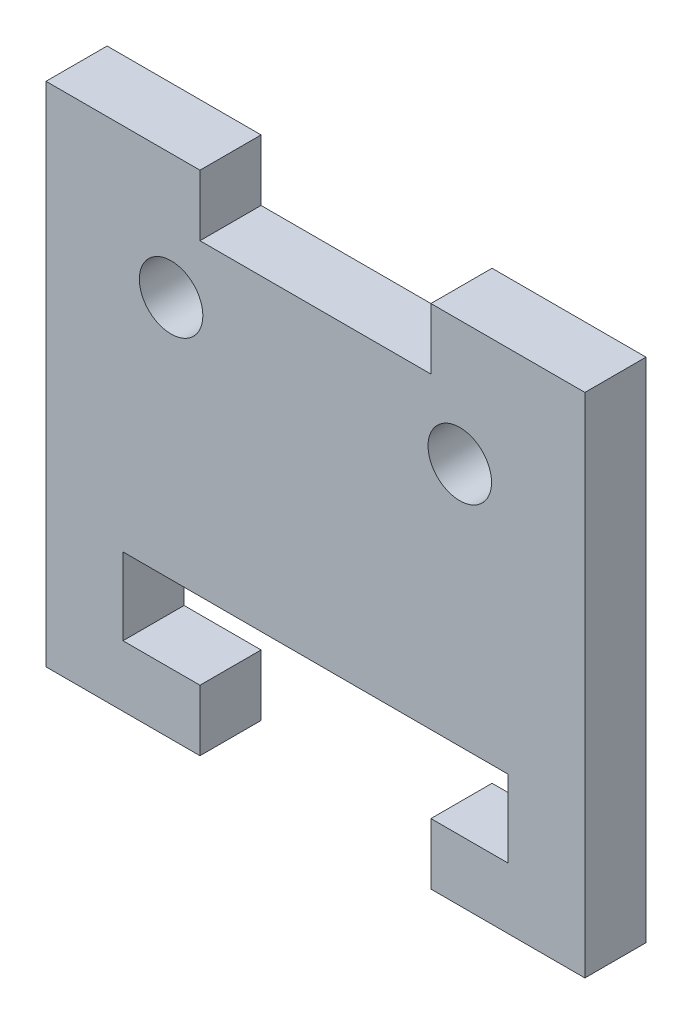
SolidWorks part; units mm, degrees
ref_plane "Front Plane" through (0, 0, 0) normal (0, 0, 1) x (1, 0, 0)
ref_plane "Top Plane" through (0, 0, 0) normal (0, 1, 0) x (1, 0, 0)
ref_plane "Right Plane" through (0, 0, 0) normal (1, 0, 0) x (0, 0, -1)
sketch "Sketch1" plane through (0, 0, 0) normal (0, 0, 1) x (1, 0, 0)
  line L0 (-14, 10) -> (-14, 13.175)
  line L1 (-14, 10) -> (14, 10) construction
  line L2 (-14, 10) -> (-14, -10)
  line L3 (-14, -10) -> (14, -10) construction
  line L4 (14, 10) -> (14, -10)
  line L5 (-14, 10) -> (14, -10) construction
  line L6 (-14, -10) -> (14, 10) construction
  line L7 (-14, 13.175) -> (-6, 13.175)
  line L8 (-6, 13.175) -> (-6, 10)
  line L9 (-6, 10) -> (6, 10)
  line L10 (6, 10) -> (6, 13.175)
  line L11 (6, 13.175) -> (14, 13.175)
  line L12 (14, 13.175) -> (14, 10)
  line L13 (-14, -10) -> (-14, -13.175)
  line L14 (-14, -13.175) -> (-6, -13.175)
  line L15 (-6, -13.175) -> (-6, -10)
  line L16 (-6, -10) -> (6, -10)
  line L17 (6, -10) -> (6, -13.175)
  line L18 (6, -13.175) -> (14, -13.175)
  line L19 (14, -13.175) -> (14, -10)
  line L21 (-10, -10) -> (10, -10)
  line L22 (-10, -10) -> (-10, -6)
  line L23 (-10, -6) -> (10, -6)
  line L24 (10, -10) -> (10, -6)
  line L25 (-10, -10) -> (10, -6) construction
  line L26 (-10, -6) -> (10, -10) construction
  circle A0 centre (7.5, 6.7) radius 1.65
  circle A1 centre (-7.5, 6.7) radius 1.65
  point P0 (0, 0)
  point P18 (0, -8)
  dimension "D1" = 3.3
  dimension "D2" = 15
  dimension "D3" = 7.5
  dimension "D4" = 20
  dimension "D5" = 3.3
  dimension "D6" = 4
  dimension "D8" = 3.175
  dimension "D9" = 20
  dimension "D10" = 10
  dimension "D11" = 28
  dimension "D12" = 8
  dimension "D13" = 12
extrude "Boss-Extrude1" add sketch "Sketch1" along normal blind 3.175 contours L24 L21 L17 L18 L19 L4 L12 L11 L10 L9 L8 L7 L0 L2 L13 L14 L15 L22 L23 A1 A0
